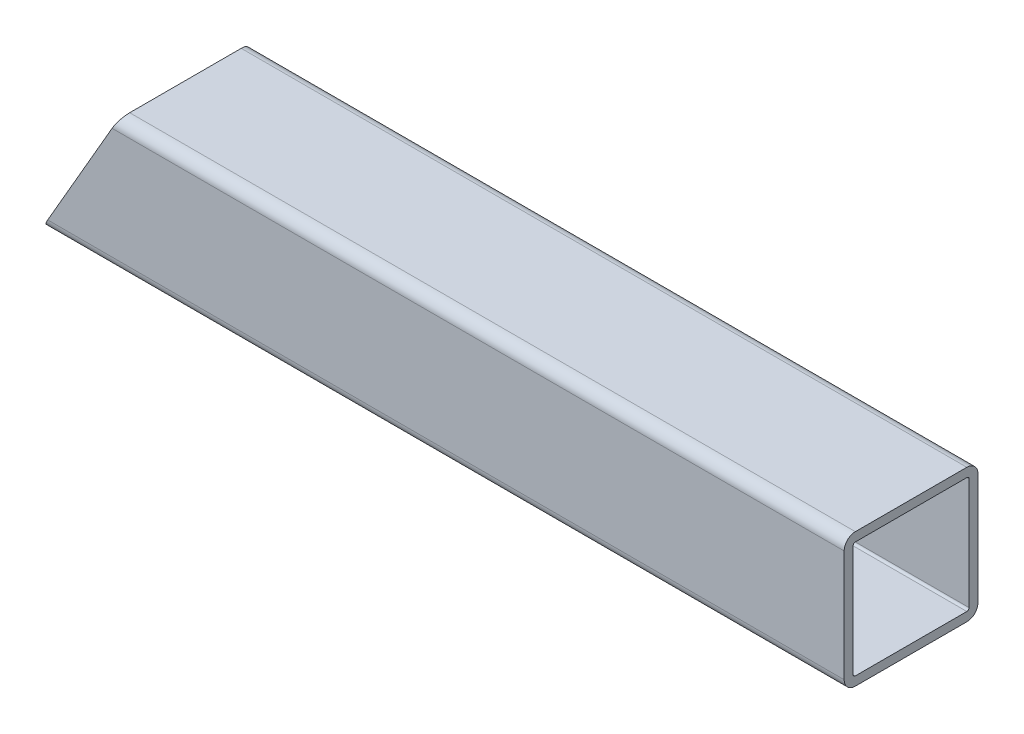
SolidWorks part; units mm, degrees
ref_plane "Front Plane" through (0, 0, 0) normal (0, 0, 1) x (1, 0, 0)
ref_plane "Top Plane" through (0, 0, 0) normal (0, 1, 0) x (1, 0, 0)
ref_plane "Right Plane" through (0, 0, 0) normal (1, 0, 0) x (0, 0, -1)
sketch "Sketch1" plane through (0, 0, 0) normal (1, 0, 0) x (0, 0, -1)
  line L1 (-15.875, 19.05) -> (15.875, 19.05)
  line L2 (-19.05, 15.875) -> (-19.05, -15.875)
  line L3 (-15.875, -19.05) -> (15.875, -19.05)
  line L4 (19.05, 15.875) -> (19.05, -15.875)
  line L5 (-19.05, 19.05) -> (19.05, -19.05) construction
  line L6 (-19.05, -19.05) -> (19.05, 19.05) construction
  arc A0 (-19.05, -15.875) -> (-15.875, -19.05) centre (-15.875, -15.875) ccw
  arc A1 (15.875, -19.05) -> (19.05, -15.875) centre (15.875, -15.875) ccw
  arc A2 (19.05, 15.875) -> (15.875, 19.05) centre (15.875, 15.875) ccw
  arc A3 (-15.875, 19.05) -> (-19.05, 15.875) centre (-15.875, 15.875) ccw
  point P0 (0, 0)
  dimension "D3" = 3.175
  dimension "D1" = 38.1
  dimension "D2" = 38.1
extrude "Extrude-Thin1" add sketch "Sketch1" along normal mid plane 228.6 thin
sketch "Sketch2" plane through (0, 0, 19.05) normal (0, 0, 1) x (1, 0, 0)
  line L0 (-114.3, -19.05) -> (-92.303, 19.05)
  line L1 (114.3, 19.05) -> (-114.3, 19.05) construction
  line L2 (-114.3, 15.875) -> (-114.3, -15.875) construction
  dimension "D1" = 30
extrude "Cut-Extrude1" cut sketch "Sketch2" against normal through all and the other way through all
